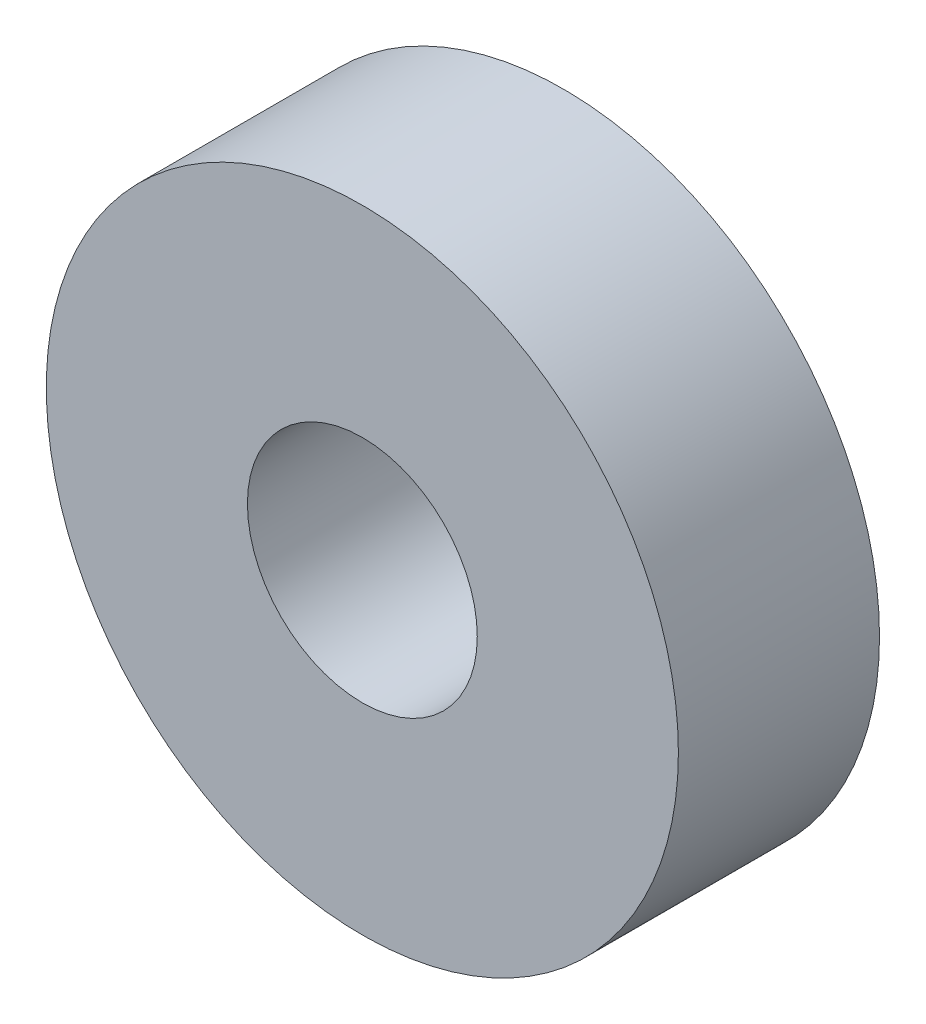
SolidWorks part; units mm, degrees
material "Plain Carbon Steel"
ref_plane "Front Plane" through (0, 0, 0) normal (0, 0, 1) x (1, 0, 0)
ref_plane "Top Plane" through (0, 0, 0) normal (0, 1, 0) x (1, 0, 0)
ref_plane "Right Plane" through (0, 0, 0) normal (1, 0, 0) x (0, 0, -1)
sketch "Sketch1" plane through (0, 0, 0) normal (0, 0, 1) x (1, 0, 0)
  circle A0 centre (0, 0) radius 4
  circle A1 centre (0, 0) radius 11
extrude "Boss-Extrude1" add sketch "Sketch1" along normal blind 7
